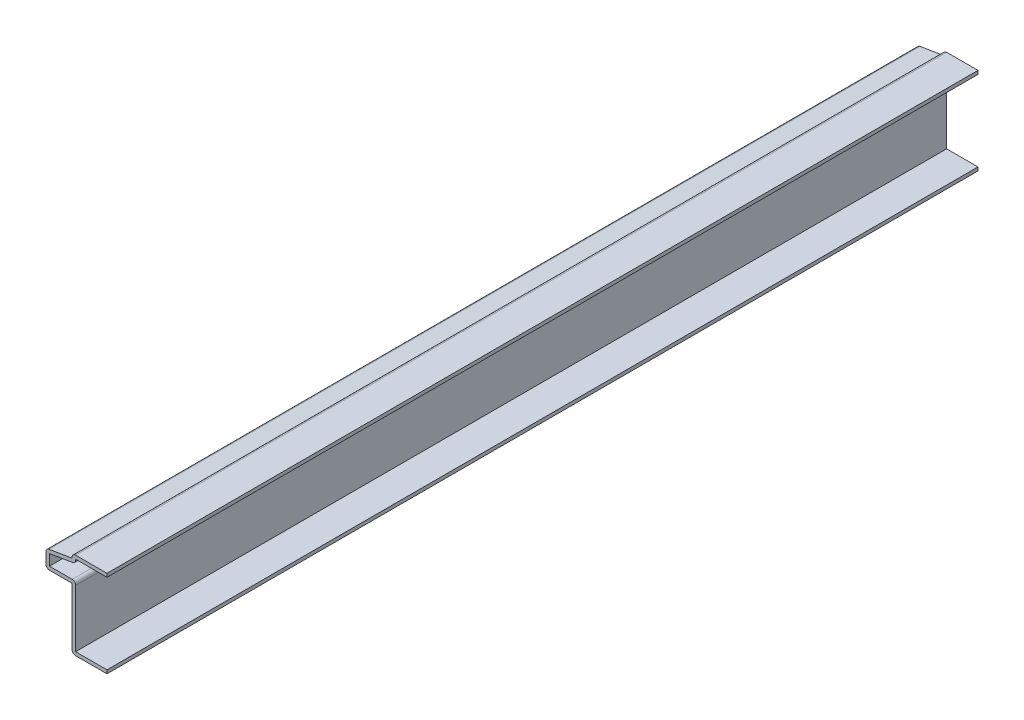
SolidWorks part; units mm, degrees
ref_plane "Front Plane" through (0, 0, 0) normal (0, 0, 1) x (1, 0, 0)
ref_plane "Top Plane" through (0, 0, 0) normal (0, 1, 0) x (1, 0, 0)
ref_plane "Right Plane" through (0, 0, 0) normal (1, 0, 0) x (0, 0, -1)
sketch "Sketch1" plane through (0, 0, 0) normal (0, 0, 1) x (1, 0, 0)
  line L0 (0, 0) -> (-12.7, 0)
  line L1 (-12.7, 0) -> (-12.7, 22.225)
  line L2 (-12.7, 22.225) -> (-22.225, 22.225)
  line L3 (-22.225, 22.225) -> (-22.225, 28.575)
  line L4 (-22.225, 28.575) -> (-12.7, 30.1625)
  line L5 (-12.7, 30.1625) -> (-12.7, 31.75)
  line L6 (-12.7, 31.75) -> (0, 31.75)
  point P9 (0, 0)
  dimension "D1" = 31.75
  dimension "D2" = 12.7
  dimension "D3" = 22.225
  dimension "D4" = 12.7
  dimension "D5" = 22.225
  dimension "D6" = 6.35
  dimension "D7" = 1.5875
extrude "Extrude-Thin1" add sketch "Sketch1" against normal blind 317.5 thin
fillet "Fillet1" radius 1.27 6 edges at (-12.7, 0, -158.75) (-22.225, 22.225, -158.75) (-11.43, 23.495, -158.75) (-11.43, 29.0866, -158.75) (-22.225, 28.575, -158.75) (-12.7, 31.75, -158.75)
